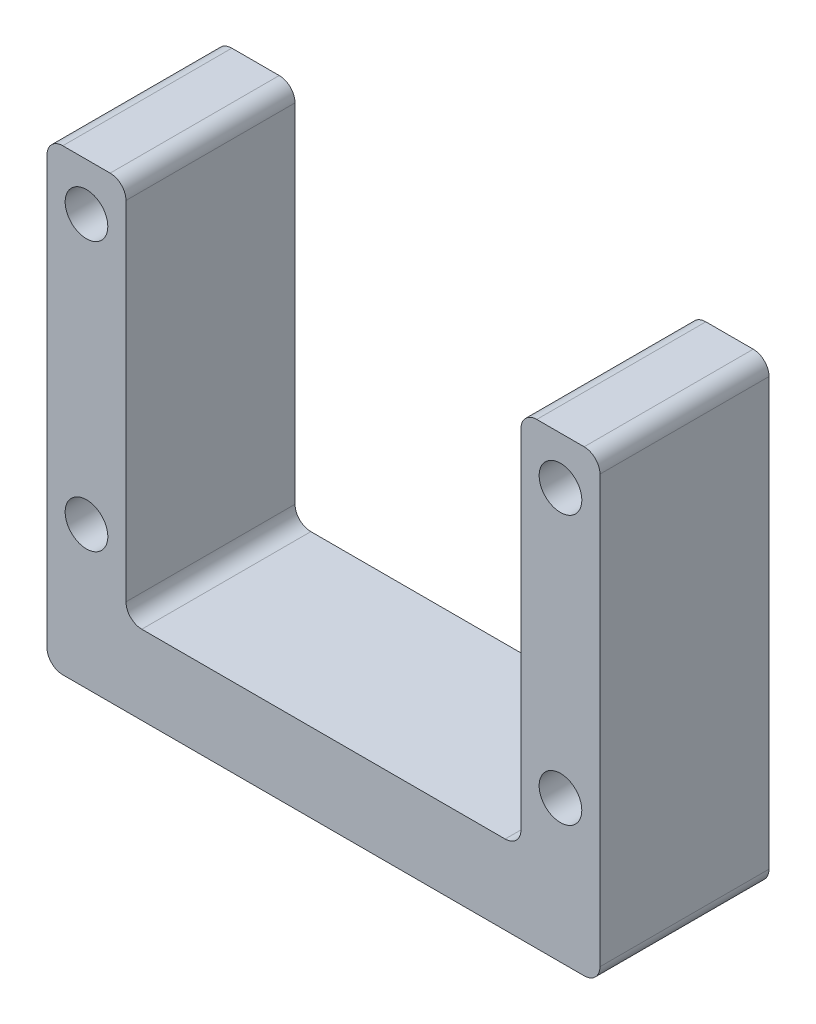
SolidWorks part; units mm, degrees
ref_plane "Plan de face" through (0, 0, 0) normal (0, 0, 1) x (1, 0, 0)
ref_plane "Plan de dessus" through (0, 0, 0) normal (0, 1, 0) x (1, 0, 0)
ref_plane "Plan de droite" through (0, 0, 0) normal (1, 0, 0) x (0, 0, -1)
sketch "Esquisse1" plane through (0, 0, 0) normal (0, 0, 1) x (1, 0, 0)
  line L0 (-12.5, 0) -> (12.5, 0)
  line L1 (12.5, 0) -> (12.5, 24)
  line L2 (12.5, 24) -> (17.5, 24)
  line L3 (17.5, 24) -> (17.5, -5)
  line L4 (17.5, -5) -> (-17.5, -5)
  line L5 (0, -5) -> (0, 0) construction
  line L6 (-17.5, 24) -> (-17.5, -5)
  line L7 (-12.5, 24) -> (-17.5, 24)
  line L8 (-12.5, 0) -> (-12.5, 24)
  dimension "D1" = 25
  dimension "D2" = 5
  dimension "D3" = 5
  dimension "D4" = 24
extrude "Boss.-Extru.1" add sketch "Esquisse1" along normal blind 10.7
sketch "Esquisse2" plane through (0, 0, 10.7) normal (0, 0, 1) x (1, 0, 0)
  line L0 (0, 0) -> (0, 12.5) construction
  line L1 (0, 12.5) -> (-16.7315, 12.5) construction
  line L2 (12.5, 0) -> (-12.5, 0) construction
  circle A0 centre (-15, 21) radius 1.35
  circle A1 centre (-15, 4) radius 1.35
  circle A2 centre (15, 4) radius 1.35
  circle A3 centre (15, 21) radius 1.35
  dimension "D1" = 17
  dimension "D2" = 30
  dimension "D3" = 2.7
  dimension "D4" = 21
extrude "Enlèv. mat.-Extru.1" cut sketch "Esquisse2" against normal through all both and the other way through all
fillet "Congé1" radius 1 8 edges at (12.5, 24, 5.35) (-12.5, 24, 5.35) (17.5, -5, 5.35) (-17.5, -5, 5.35) (-17.5, 24, 5.35) (17.5, 24, 5.35) (12.5, 0, 5.35) (-12.5, 0, 5.35)
